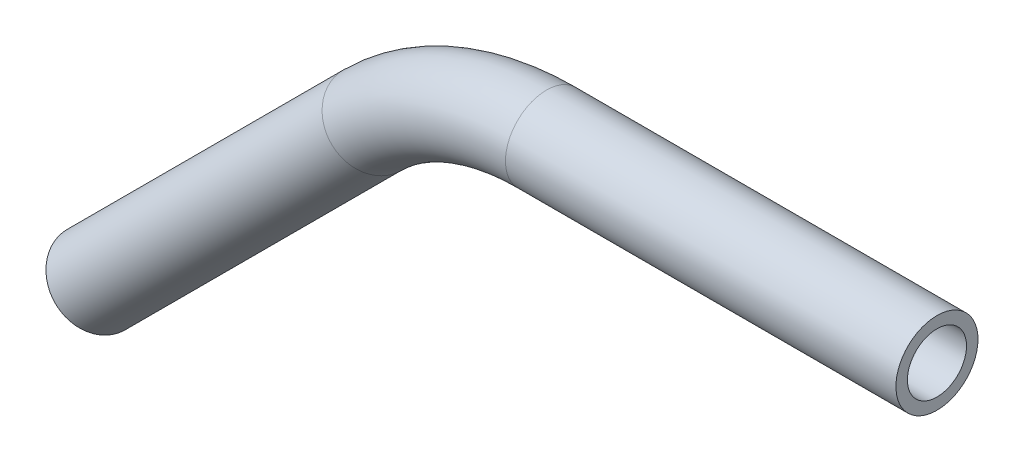
SolidWorks part; units mm, degrees
material "AISI 316 Stainless Steel Sheet (SS)"
ref_plane "Front Plane" through (0, 0, 0) normal (0, 0, 1) x (1, 0, 0)
ref_plane "Top Plane" through (0, 0, 0) normal (0, 1, 0) x (1, 0, 0)
ref_plane "Right Plane" through (0, 0, 0) normal (1, 0, 0) x (0, 0, -1)
sketch "Sketch1" plane through (0, 0, 0) normal (0, 0, 1) x (1, 0, 0)
  line L0 (-22.4376, -22.4376) -> (-1.0764, -1.0764)
  line L1 (12.3939, 4.5032) -> (42.6032, 4.5032)
  arc A0 (-1.0764, -1.0764) -> (12.3939, 4.5032) centre (12.3939, -14.5468) cw
  point P6 (4.5032, 4.5032)
  dimension "D3" = 19.05
  dimension "D4" = 45
  dimension "D1" = 38.1
  dimension "D2" = 38.1
ref_plane "Plane1" through (42.6032, 4.5032, 0) normal (1, 0, 0) x (0, 0, -1)
sketch "Sketch2" plane through (42.6032, 4.5032, 0) normal (1, 0, 0) x (0, 0, -1)
  circle A0 centre (0, 0) radius 3.175
  circle A1 centre (0, 0) radius 2.286
  dimension "D1" = 6.35
  dimension "D2" = 4.572
sweep "Sweep1" add profiles "Sketch2" path "Sketch1"
